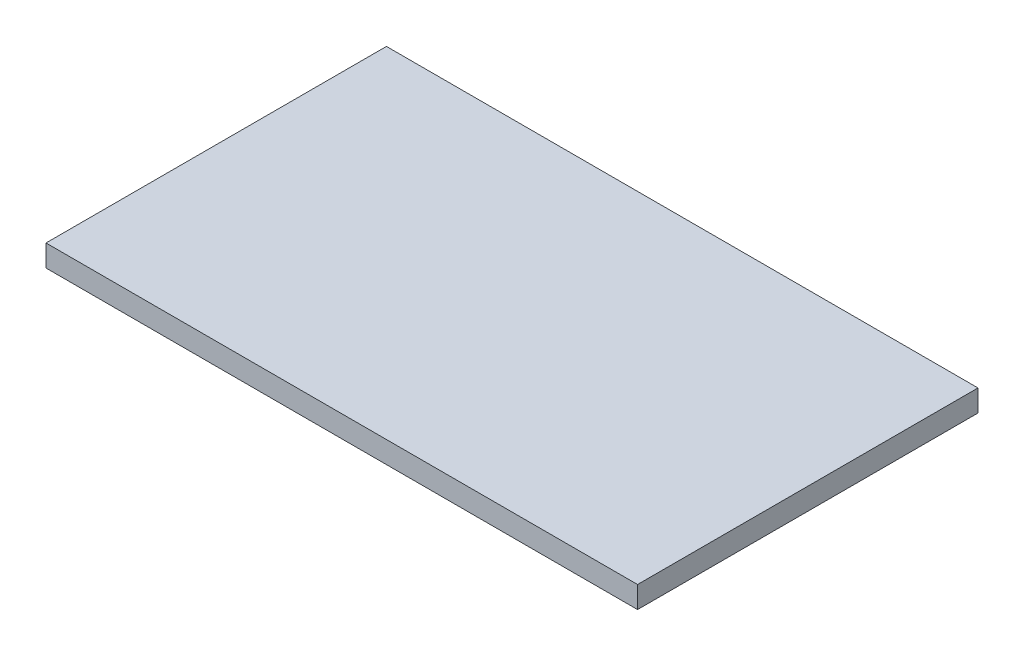
SolidWorks part; units mm, degrees
ref_plane "Спереди" through (0, 0, 0) normal (0, 0, 1) x (1, 0, 0)
ref_plane "Сверху" through (0, 0, 0) normal (0, 1, 0) x (1, 0, 0)
ref_plane "Справа" through (0, 0, 0) normal (1, 0, 0) x (0, 0, -1)
sketch "Эскиз1" plane through (0, 0, 0) normal (0, 1, 0) x (1, 0, 0)
  line L1 (245, -141) -> (-245, -141)
  line L2 (245, -141) -> (245, 141)
  line L3 (245, 141) -> (-245, 141)
  line L4 (-245, -141) -> (-245, 141)
  line L5 (245, -141) -> (-245, 141) construction
  line L6 (245, 141) -> (-245, -141) construction
  point P0 (0, 0)
  dimension "D1" = 490
  dimension "D2" = 282
extrude "Бобышка-Вытянуть1" add sketch "Эскиз1" along normal blind 18
